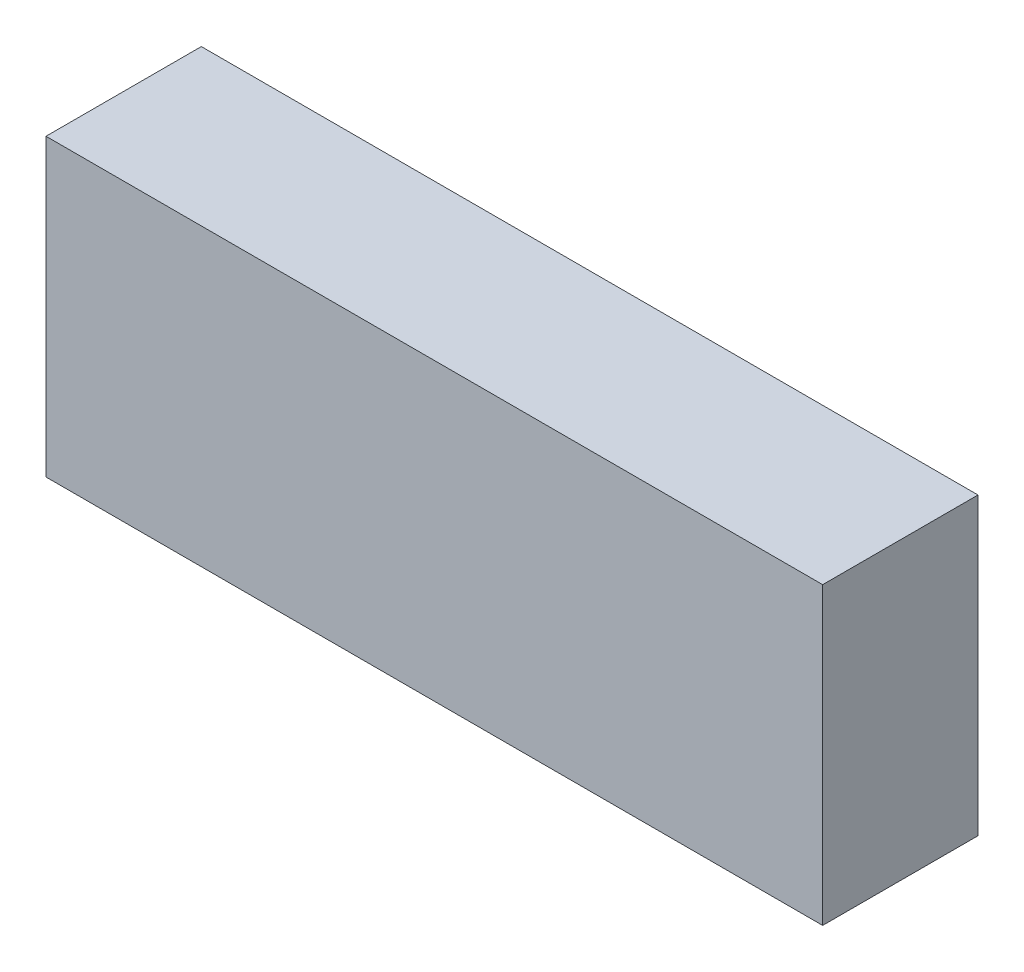
SolidWorks part; units mm, degrees
ref_plane "Front Plane" through (0, 0, 0) normal (0, 0, 1) x (1, 0, 0)
ref_plane "Top Plane" through (0, 0, 0) normal (0, 1, 0) x (1, 0, 0)
ref_plane "Right Plane" through (0, 0, 0) normal (1, 0, 0) x (0, 0, -1)
sketch "Sketch1" plane through (0, 0, 0) normal (0, 0, 1) x (1, 0, 0)
  line L1 (-25, -9.5) -> (25, -9.5)
  line L2 (-25, -9.5) -> (-25, 9.5)
  line L3 (-25, 9.5) -> (25, 9.5)
  line L4 (25, -9.5) -> (25, 9.5)
  line L5 (-25, -9.5) -> (25, 9.5) construction
  line L6 (-25, 9.5) -> (25, -9.5) construction
  point P0 (0, 0)
  dimension "D1" = 50
  dimension "D2" = 19
extrude "Boss-Extrude1" add sketch "Sketch1" along normal blind 10
